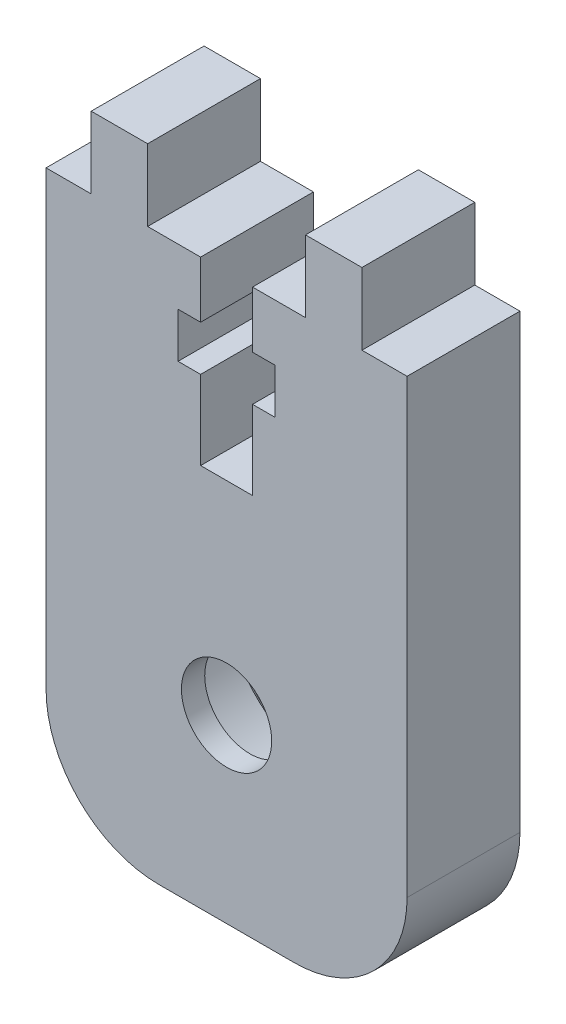
SolidWorks part; units mm, degrees
ref_plane "Front Plane" through (0, 0, 0) normal (0, 0, 1) x (1, 0, 0)
ref_plane "Top Plane" through (0, 0, 0) normal (0, 1, 0) x (1, 0, 0)
ref_plane "Right Plane" through (0, 0, 0) normal (1, 0, 0) x (0, 0, -1)
sketch "Sketch1" plane through (0, 0, 0) normal (0, 0, 1) x (1, 0, 0)
  line L0 (7.998, 12.5) -> (5.998, 12.5)
  line L1 (7.998, -12.5) -> (-7.998, -12.5)
  line L2 (7.998, -12.5) -> (7.998, 12.5)
  line L3 (7.998, 12.5) -> (-7.998, 12.5) construction
  line L4 (-7.998, -12.5) -> (-7.998, 12.5)
  line L5 (7.998, -12.5) -> (-7.998, 12.5) construction
  line L6 (7.998, 12.5) -> (-7.998, -12.5) construction
  line L7 (5.998, 12.5) -> (3.498, 12.5) construction
  line L8 (5.998, 12.5) -> (5.998, 15.675)
  line L9 (5.998, 15.675) -> (3.498, 15.675)
  line L10 (3.498, 12.5) -> (3.498, 15.675)
  line L11 (-3.498, 12.5) -> (-5.998, 12.5) construction
  line L12 (-3.498, 12.5) -> (-3.498, 15.675)
  line L13 (-3.498, 15.675) -> (-5.998, 15.675)
  line L14 (-5.998, 12.5) -> (-5.998, 15.675)
  line L15 (-5.998, 12.5) -> (-7.998, 12.5)
  line L16 (3.498, 12.5) -> (-3.498, 12.5) construction
  line L17 (1.15, 12.5) -> (3.498, 12.5)
  line L18 (1.15, 12.5) -> (-1.15, 12.5) construction
  line L19 (1.15, 12.5) -> (1.15, 10)
  line L20 (1.15, 4.5) -> (-1.15, 4.5)
  line L21 (-1.15, 12.5) -> (-1.15, 10)
  line L22 (2.15, 10) -> (1.15, 10)
  line L23 (2.15, 10) -> (2.15, 8)
  line L24 (2.15, 8) -> (1.15, 8)
  line L25 (-2.15, 10) -> (-2.15, 8)
  line L26 (-1.15, 12.5) -> (-3.498, 12.5)
  line L27 (-1.15, 10) -> (-2.15, 10)
  line L28 (-1.15, 8) -> (-2.15, 8)
  line L29 (1.15, 8) -> (1.15, 4.5)
  line L30 (-1.15, 8) -> (-1.15, 4.5)
  circle A1 centre (0, -4.5) radius 4.9 construction
  point P0 (0, 0)
  point P25 (0, 12.5)
  point P26 (0, 4.5)
  dimension "D2" = 17
  dimension "D1" = 9.8
  dimension "D3" = 15.996
  dimension "D4" = 25
  dimension "D5" = 3.175
  dimension "D6" = 2.5
  dimension "D7" = 2
  dimension "D8" = 2.3
  dimension "D9" = 2
  dimension "D10" = 4.3
  dimension "D11" = 8
  dimension "D12" = 2.5
extrude "Boss-Extrude1" add sketch "Sketch1" along normal blind 5
sketch "Sketch2" plane through (0, 0, 0) normal (0, 0, -1) x (-1, 0, 0)
  circle A0 centre (0, -4.5) radius 4.9
  circle A1 centre (0, -4.5) radius 4.9 construction
extrude "Cut-Extrude1" cut sketch "Sketch2" against normal blind 3.9688
sketch "Sketch3" plane through (0, 0, 3.9688) normal (0, 0, -1) x (-1, 0, 0)
  circle A0 centre (0, -4.5) radius 2
  dimension "D1" = 4
extrude "Cut-Extrude2" cut sketch "Sketch3" against normal up to next
fillet "Fillet1" radius 5 2 edges at (-7.998, -12.5, 2.5) (7.998, -12.5, 2.5)
chamfer "Chamfer1" distance 0.2 angle 45 1 edges at (-4.9, -4.5, 0)
ref_axis "Axis1" through (0, -4.5, 5) along (0, 0, -1)
sketch "Sketch5" plane through (0, 0, 0) normal (1, 0, 0) x (0, 0, -1)
  line L0 (-5, -4.5) -> (-3.9688, -4.5) construction
  line L1 (-3.9688, -6.5) -> (-3.9688, -2.5) construction
  circle A0 centre (-3.8688, -9.3) radius 0.15
  dimension "D2" = 0.1
  dimension "D3" = 0.3
  dimension "D1" = 4.8
revolve "Cut-Revolve1" cut sketch "Sketch5" angle 360 about axis through (0, -4.5, 5) along (0, 0, -1)
